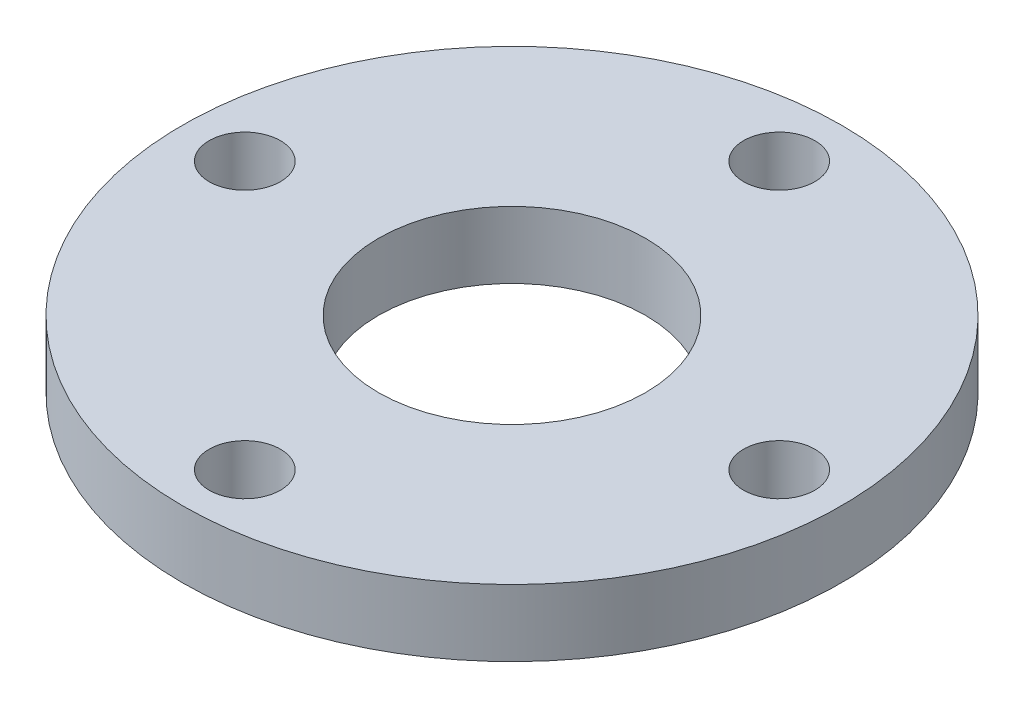
SolidWorks part; units mm, degrees
ref_plane "前视基准面" through (0, 0, 0) normal (0, 0, 1) x (1, 0, 0)
ref_plane "上视基准面" through (0, 0, 0) normal (0, 1, 0) x (1, 0, 0)
ref_plane "右视基准面" through (0, 0, 0) normal (1, 0, 0) x (0, 0, -1)
other "Configuration Table"
sketch "草图1" plane through (0, 0, 0) normal (0, 1, 0) x (1, 0, 0)
  circle A0 centre (0, 0) radius 14.8
  circle A1 centre (0, 0) radius 6
  circle A2 centre (12, 0) radius 1.6
  circle A3 centre (0, -12) radius 1.6
  circle A4 centre (-12, 0) radius 1.6
  circle A5 centre (0, 12) radius 1.6
  point P15 (0, 0)
  dimension "D1" = 4
extrude "凸台-拉伸1" add sketch "草图1" along normal blind 3
